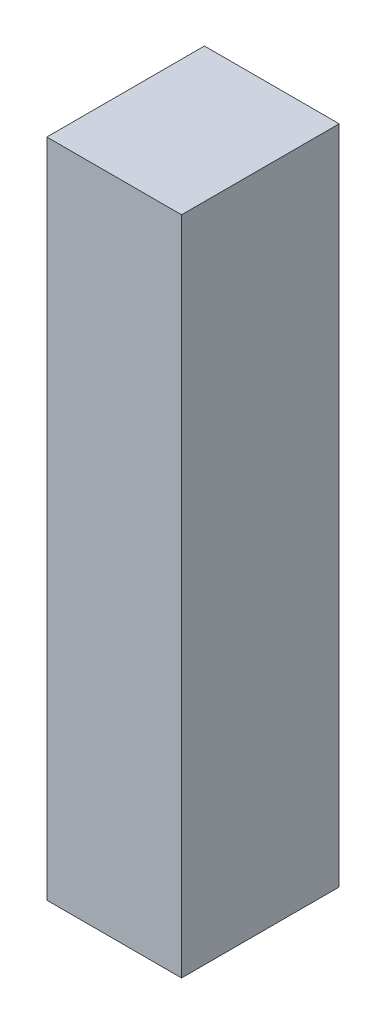
SolidWorks part; units mm, degrees
ref_plane "Front Plane" through (0, 0, 0) normal (0, 0, 1) x (1, 0, 0)
ref_plane "Top Plane" through (0, 0, 0) normal (0, 1, 0) x (1, 0, 0)
ref_plane "Right Plane" through (0, 0, 0) normal (1, 0, 0) x (0, 0, -1)
sketch "Sketch1" plane through (0, 0, 0) normal (0, 1, 0) x (1, 0, 0)
  line L1 (0, 0) -> (5.3, 0)
  line L2 (0, 0) -> (0, 6.2)
  line L3 (0, 6.2) -> (5.3, 6.2)
  line L4 (5.3, 0) -> (5.3, 6.2)
  dimension "D1" = 6.2
  dimension "D2" = 5.3
extrude "Boss-Extrude1" add sketch "Sketch1" along normal blind 26
sketch "Sketch2" plane through (0, 0, -6.2) normal (0, 0, -1) x (-1, 0, 0)
  line L0 (-5.3, 26) -> (-5.3, 0) construction
  text T0 "97"
extrude "Cut-Extrude1" cut sketch "Sketch2" against normal blind 1
